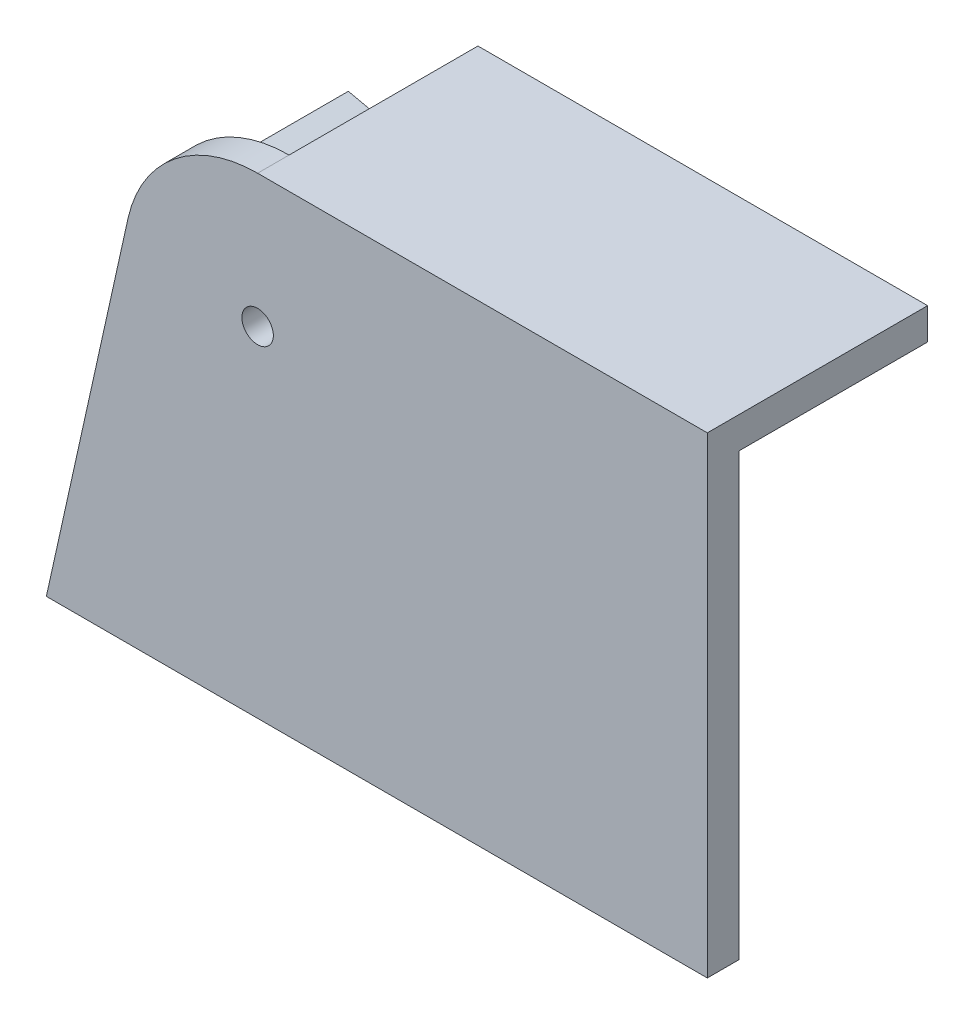
SolidWorks part; units mm, degrees
ref_plane "Front Plane" through (0, 0, 0) normal (0, 0, 1) x (1, 0, 0)
ref_plane "Top Plane" through (0, 0, 0) normal (0, 1, 0) x (1, 0, 0)
ref_plane "Right Plane" through (0, 0, 0) normal (1, 0, 0) x (0, 0, -1)
sketch "Sketch1" plane through (0, 0, 0) normal (0, 0, 1) x (1, 0, 0)
  line L0 (-92.0296, 58.4769) -> (-105, 0)
  line L1 (0, 0) -> (-105, 0)
  line L2 (0, 0) -> (0, 75)
  line L3 (0, 75) -> (-71.44, 75)
  arc A0 (-71.44, 75) -> (-92.0296, 58.4769) centre (-71.44, 53.91) ccw
  circle A1 centre (-71.44, 53.91) radius 2.5
  point P8 (-71.44, 53.91)
  dimension "D5" = 5
  dimension "D1" = 75
  dimension "D2" = 105
  dimension "D3" = 53.91
  dimension "D4" = 71.44
extrude "Boss-Extrude1" add sketch "Sketch1" along normal blind 5
sketch "Sketch2" plane through (0, 0, 5) normal (0, 0, 1) x (1, 0, 0)
  line L0 (-105, 0) -> (-92.0296, 58.4769)
  line L1 (-92.0296, 58.4769) -> (-87.1482, 57.3941)
  line L2 (-87.1482, 57.3941) -> (-99.8785, 0)
  line L3 (-105, 0) -> (0, 0) construction
  line L4 (-99.8785, 0) -> (-105, 0)
  line L5 (0, 75) -> (-71.44, 75) construction
  line L6 (0, 75) -> (-71.44, 75)
  line L7 (0, 75) -> (0, 70)
  line L8 (0, 70) -> (-71.44, 70)
  line L9 (-71.44, 75) -> (-71.44, 70)
  point P13 (-64.7673, 75)
  dimension "D1" = 5
  dimension "D2" = 5
extrude "Boss-Extrude2" add sketch "Sketch2" against normal blind 35
